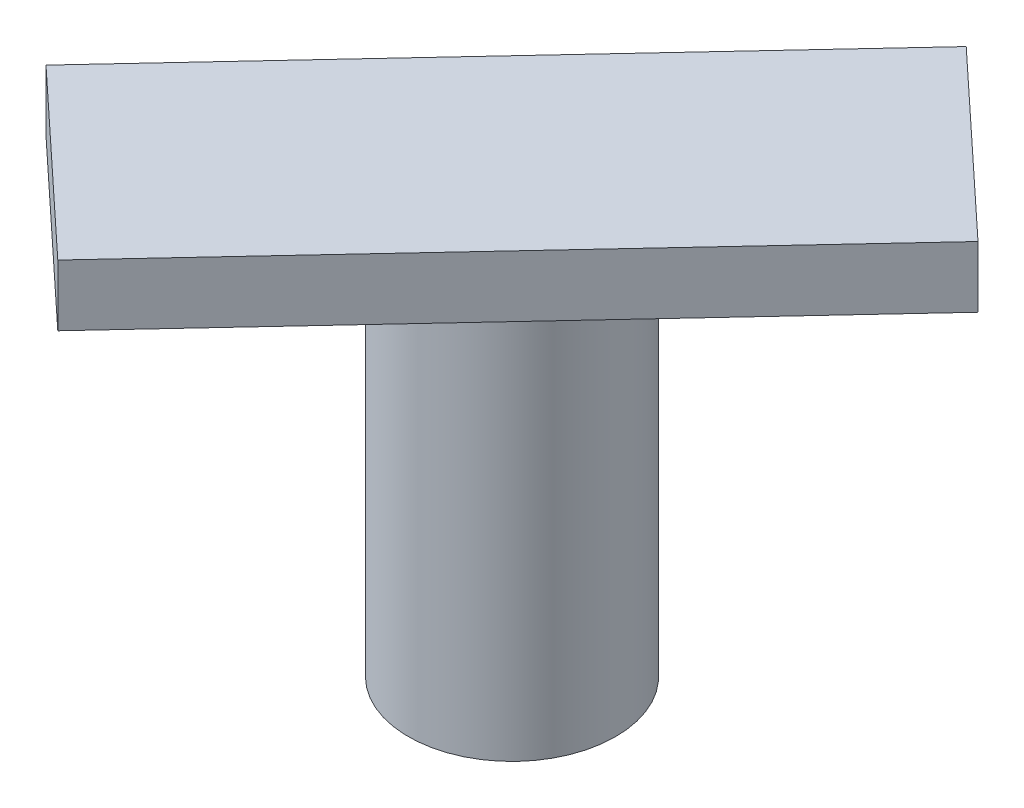
SolidWorks part; units mm, degrees
ref_plane "Front Plane" through (0, 0, 0) normal (0, 0, 1) x (1, 0, 0)
ref_plane "Top Plane" through (0, 0, 0) normal (0, 1, 0) x (1, 0, 0)
ref_plane "Right Plane" through (0, 0, 0) normal (1, 0, 0) x (0, 0, -1)
sketch "Sketch1" plane through (0, 0, 0) normal (0, 1, 0) x (1, 0, 0)
  circle A0 centre (22.7298, -8.2396) radius 16.9166
extrude "Boss-Extrude1" add sketch "Sketch1" along normal blind 64
sketch "Sketch2" plane through (0, 64, 0) normal (0, 1, 0) x (1, 0, 0)
  line L1 (-30.4017, -27.7334) -> (75.8613, -27.7334)
  line L2 (-30.4017, -27.7334) -> (-30.4017, 11.2543)
  line L3 (-30.4017, 11.2543) -> (75.8613, 11.2543)
  line L4 (75.8613, -27.7334) -> (75.8613, 11.2543)
  line L5 (-30.4017, -27.7334) -> (75.8613, 11.2543) construction
  line L6 (-30.4017, 11.2543) -> (75.8613, -27.7334) construction
  circle A0 centre (22.7298, -8.2396) radius 16.9166 construction
  point P0 (22.7298, -8.2396)
extrude "Boss-Extrude2" add sketch "Sketch2" along normal blind 10
move or copy body "Body-Move/Copy1" bodies to move or copy 102 copy no rotation origin (22.7298, 0, 8.2396) rotation axis (0, 1, 0) rotation angle 47
